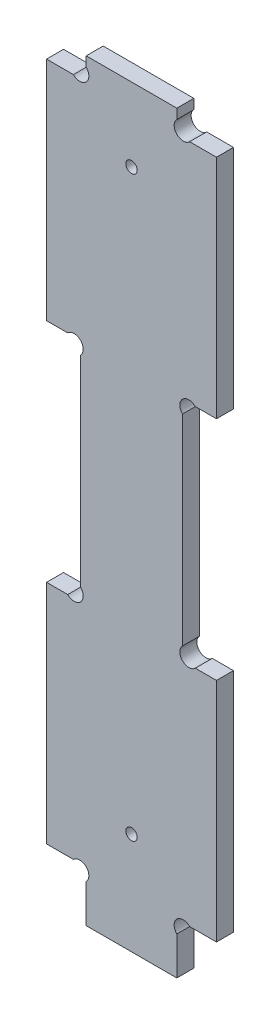
SolidWorks part; units mm, degrees
ref_plane "Plan de face" through (0, 0, 0) normal (0, 0, 1) x (1, 0, 0)
ref_plane "Plan de dessus" through (0, 0, 0) normal (0, 1, 0) x (1, 0, 0)
ref_plane "Plan de droite" through (0, 0, 0) normal (1, 0, 0) x (0, 0, -1)
sketch "Esquisse1" plane through (0, 0, 0) normal (0, 0, 1) x (1, 0, 0)
  line L14 (25.2627, 9) -> (30, 9)
  line L16 (30, 49) -> (30, 9)
  line L17 (26.2627, 49) -> (30, 49)
  line L18 (25.2627, 129) -> (30, 129)
  line L19 (30, 89) -> (30, 129)
  line L20 (26.2627, 89) -> (30, 89)
  line L21 (3.7373, 89) -> (0, 89)
  line L22 (0, 89) -> (0, 129)
  line L23 (4.7373, 129) -> (0, 129)
  line L24 (3.7373, 49) -> (0, 49)
  line L25 (0, 49) -> (0, 9)
  line L26 (4.7373, 9) -> (0, 9)
  line L27 (23, 131.2627) -> (23, 133)
  line L28 (23, 6.7373) -> (23, 0)
  line L29 (24, 86.7373) -> (24, 51.2627)
  line L30 (7, 131.2627) -> (7, 133)
  line L31 (6, 86.7373) -> (6, 51.2627)
  line L32 (7, 6.7373) -> (7, 0)
  line L33 (7, 133) -> (23, 133)
  line L34 (7, 0) -> (23, 0)
  arc A1 (25.2627, 9) -> (23, 6.7373) centre (24.1314, 7.8686) ccw
  arc A2 (24, 51.2627) -> (26.2627, 49) centre (25.1314, 50.1314) ccw
  arc A3 (25.2627, 129) -> (23, 131.2627) centre (24.1314, 130.1314) cw
  arc A5 (24, 86.7373) -> (26.2627, 89) centre (25.1314, 87.8686) cw
  arc A6 (6, 86.7373) -> (3.7373, 89) centre (4.8686, 87.8686) ccw
  arc A8 (4.7373, 129) -> (7, 131.2627) centre (5.8686, 130.1314) ccw
  arc A9 (6, 51.2627) -> (3.7373, 49) centre (4.8686, 50.1314) cw
  arc A10 (4.7373, 9) -> (7, 6.7373) centre (5.8686, 7.8686) cw
  dimension "D13" = 6
  dimension "D14" = 30
  dimension "D20" = 1.6
  dimension "D1" = 40
  dimension "D2" = 40
  dimension "D3" = 40
  dimension "D4" = 4
  dimension "D5" = 9
  dimension "D6" = 30
  dimension "D7" = 16
  dimension "D8" = 18
  dimension "D9" = 16
  dimension "D10" = 7
  dimension "D11" = 7
  dimension "D12" = 6
  dimension "D15" = 1.1314
  dimension "D16" = 1.1314
  dimension "D17" = 2.2627
  dimension "D18" = 2.2627
  dimension "D19" = 7
  dimension "D21" = 1.1314
  dimension "D22" = 1.1314
  dimension "D23" = 2.2627
  dimension "D24" = 2.2627
  dimension "D25" = 1.1314
  dimension "D26" = 2.2627
  dimension "D27" = 2.2627
  dimension "D28" = 1.1314
  dimension "D29" = 1.1314
  dimension "D30" = 1.1314
  dimension "D31" = 2.2627
  dimension "D32" = 2.2627
extrude "Extrusion1" add sketch "Esquisse1" along normal blind 3
sketch "Esquisse2" plane through (0, 0, 3) normal (0, 0, 1) x (1, 0, 0)
  line L0 (25.2627, 9) -> (30, 9) construction
  line L1 (7, 0) -> (23, 0) construction
  line L2 (4.7373, 129) -> (0, 129) construction
  circle A0 centre (15, 18) radius 1
  circle A1 centre (15, 120) radius 1
  point P4 (15, 0)
  point P9 (0, 0)
  dimension "D2" = 2
  dimension "D1" = 9
  dimension "D3" = 9
extrude "Enlèv. mat.-Extru.1" cut sketch "Esquisse2" against normal through all
